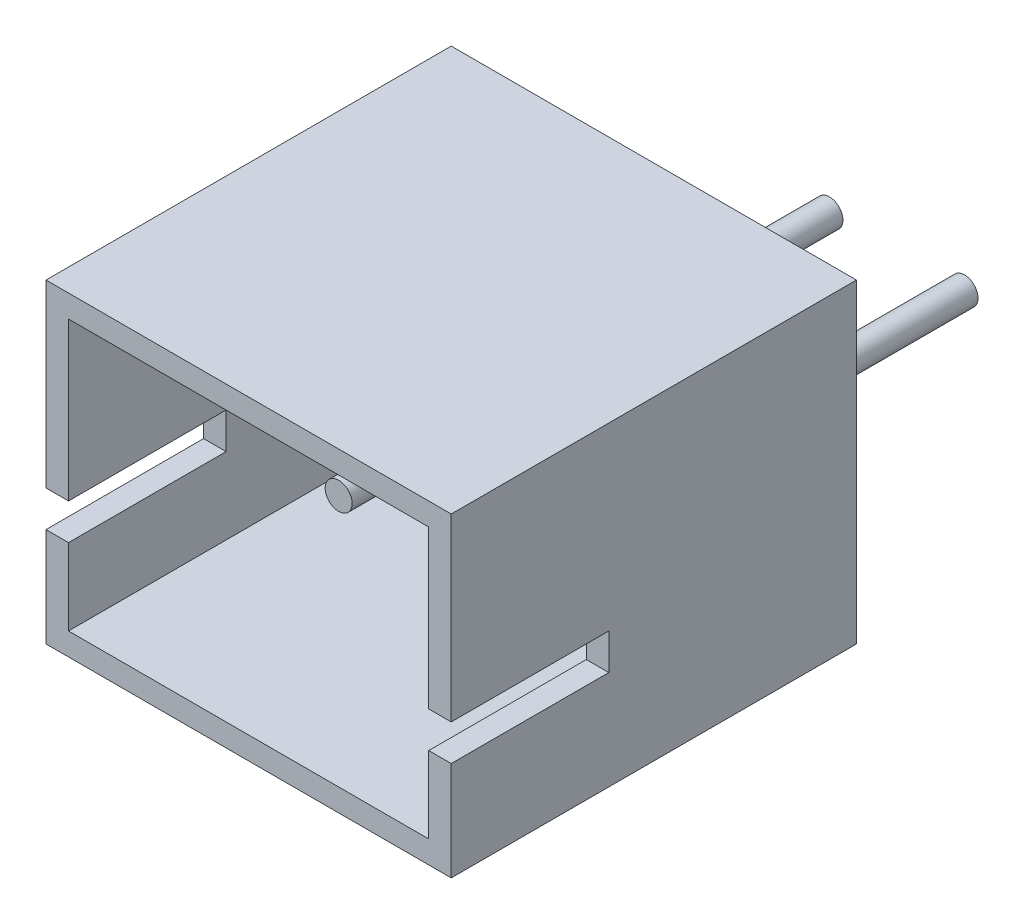
SolidWorks part; units mm, degrees
ref_plane "Front Plane" through (0, 0, 0) normal (0, 0, 1) x (1, 0, 0)
ref_plane "Top Plane" through (0, 0, 0) normal (0, 1, 0) x (1, 0, 0)
ref_plane "Right Plane" through (0, 0, 0) normal (1, 0, 0) x (0, 0, -1)
sketch "Sketch1" plane through (0, 0, 0) normal (0, 0, 1) x (1, 0, 0)
  line L1 (-2.25, 1.75) -> (2.25, 1.75)
  line L2 (-2.25, 1.75) -> (-2.25, -1.75)
  line L3 (-2.25, -1.75) -> (2.25, -1.75)
  line L4 (2.25, 1.75) -> (2.25, -1.75)
  line L5 (-2.25, 1.75) -> (2.25, -1.75) construction
  line L6 (-2.25, -1.75) -> (2.25, 1.75) construction
  point P0 (0, 0)
  dimension "D1" = 3.5
  dimension "D2" = 4.5
extrude "Boss-Extrude1" add sketch "Sketch1" along normal blind 4.5
sketch "Sketch2" plane through (0, 0, 4.5) normal (0, 0, 1) x (1, 0, 0)
  line L1 (-2, 1.5) -> (2, 1.5)
  line L2 (-2, 1.5) -> (-2, -1.5)
  line L3 (-2, -1.5) -> (2, -1.5)
  line L4 (2, 1.5) -> (2, -1.5)
  line L5 (-2, 1.5) -> (2, -1.5) construction
  line L6 (-2, -1.5) -> (2, 1.5) construction
  point P0 (0, 0)
  dimension "D1" = 4
  dimension "D2" = 3
extrude "Cut-Extrude1" cut sketch "Sketch2" against normal blind 4.25
sketch "Sketch3" plane through (0, 0, 0) normal (0, 0, -1) x (-1, 0, 0)
  line L0 (0, 0) -> (0, 1.75) construction
  line L1 (-2.25, 1.75) -> (2.25, 1.75) construction
  line L2 (0, 1.75) -> (0, -1.75) construction
  line L3 (2.25, -1.75) -> (-2.25, -1.75) construction
  line L4 (-2.25, -0.45) -> (2.25, -0.45) construction
  line L5 (-2.25, -1.75) -> (-2.25, 1.75) construction
  line L6 (2.25, 1.75) -> (2.25, -1.75) construction
  circle A0 centre (-0.75, -0.45) radius 0.15
  circle A1 centre (0.75, -0.45) radius 0.15
  point P16 (0, -0.45)
  dimension "D3" = 0.3
  dimension "D1" = 2.2
  dimension "D2" = 0.75
extrude "Boss-Extrude2" add sketch "Sketch3" along normal blind 2.7 and the other way blind 4
sketch "Sketch4" plane through (-2.25, 0, 0) normal (-1, 0, 0) x (0, 0, 1)
  line L0 (-2.7, -0.45) -> (4.5, -0.45) construction
  line L1 (-2.7, -0.3) -> (-2.7, -0.6) construction
  line L2 (4.5, 1.75) -> (4.5, -1.75) construction
  line L4 (6.25, -0.25) -> (2.75, -0.25)
  line L5 (6.25, -0.25) -> (6.25, -0.65)
  line L6 (6.25, -0.65) -> (2.75, -0.65)
  line L7 (2.75, -0.25) -> (2.75, -0.65)
  line L8 (6.25, -0.25) -> (2.75, -0.65) construction
  line L9 (6.25, -0.65) -> (2.75, -0.25) construction
  dimension "D1" = 0.4
  dimension "D2" = 3.5
extrude "Cut-Extrude2" cut sketch "Sketch4" against normal through all
